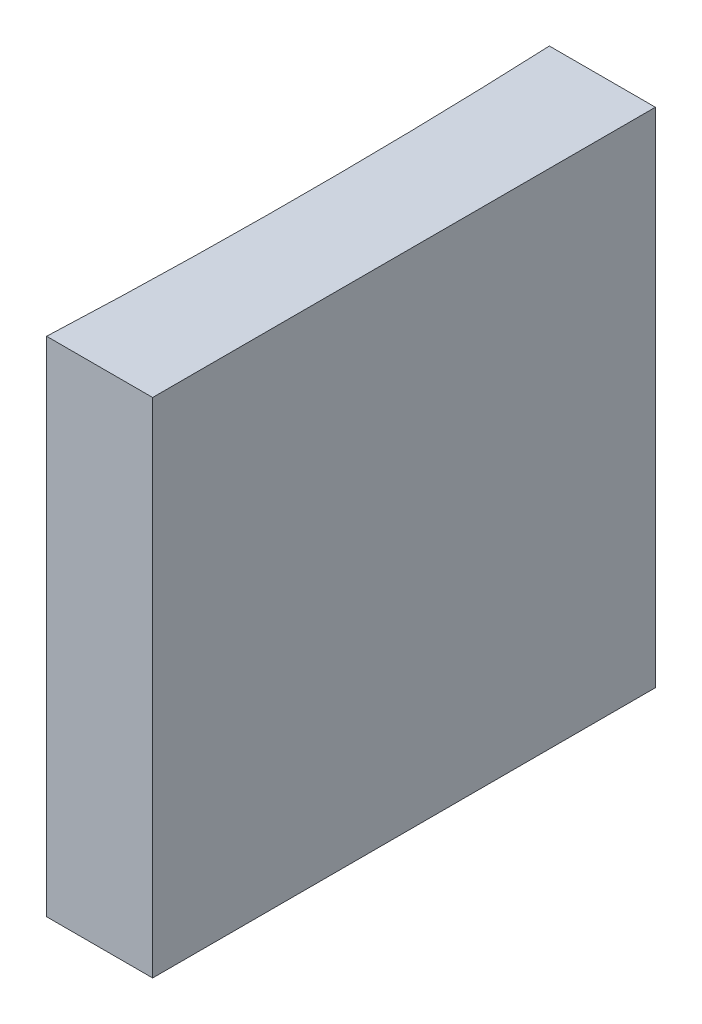
SolidWorks part; units mm, degrees
ref_plane "前视基准面" through (0, 0, 0) normal (0, 0, 1) x (1, 0, 0)
ref_plane "上视基准面" through (0, 0, 0) normal (0, 1, 0) x (1, 0, 0)
ref_plane "右视基准面" through (0, 0, 0) normal (1, 0, 0) x (0, 0, -1)
sketch "草图1" plane through (0, 0, 0) normal (0, 1, 0) x (1, 0, 0)
  line L0 (0, 0) -> (0, -10)
  line L1 (0, 0) -> (-2.1091, 0)
  line L2 (0, -10) -> (-2.1091, -10)
  line L3 (21.2259, -5) -> (-21.2259, -5) construction
  arc A0 (-2.1091, -10) -> (-2.1091, 0) centre (-116.62, -5) ccw
  point P7 (-2, -5)
  point P8 (0, -5)
  dimension "D2" = 114.62
  dimension "D3" = 2
  dimension "D1" = 10
extrude "凸台-拉伸1" add sketch "草图1" along normal blind 10
